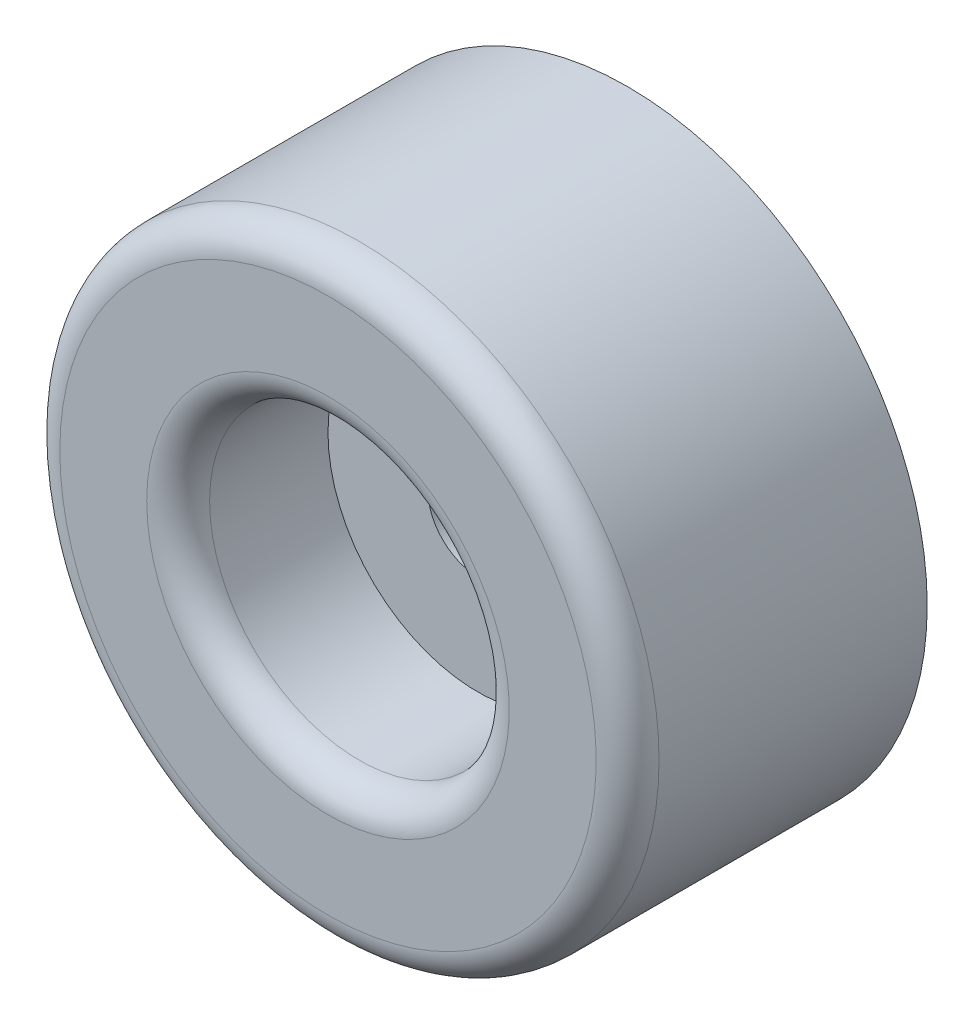
SolidWorks part; units mm, degrees
material "EPDM 60 Durometer"
ref_plane "Front Plane" through (0, 0, 0) normal (0, 0, 1) x (1, 0, 0)
ref_plane "Top Plane" through (0, 0, 0) normal (0, 1, 0) x (1, 0, 0)
ref_plane "Right Plane" through (0, 0, 0) normal (1, 0, 0) x (0, 0, -1)
sketch "Sketch1" plane through (0, 0, 0) normal (1, 0, 0) x (0, 0, -1)
  line L0 (0, 3.175) -> (0, 19.05)
  line L1 (0, 19.05) -> (-19.05, 19.05)
  line L2 (-19.05, 19.05) -> (-19.05, 9.525)
  line L3 (-19.05, 9.525) -> (-9.525, 9.525)
  line L4 (-9.525, 9.525) -> (-9.525, 3.175)
  line L5 (-13.1473, 0) -> (0, 0) construction
  line L6 (-9.525, 3.175) -> (0, 3.175)
  dimension "D1" = 19.05
  dimension "D2" = 19.05
  dimension "D3" = 3.175
  dimension "D4" = 9.525
  dimension "D5" = 9.525
revolve "Revolve1" add sketch "Sketch1" angle 360 about L5
fillet "Fillet1" radius 2 2 edges at (9.525, 0, 19.05) (19.05, 0, 19.05)
